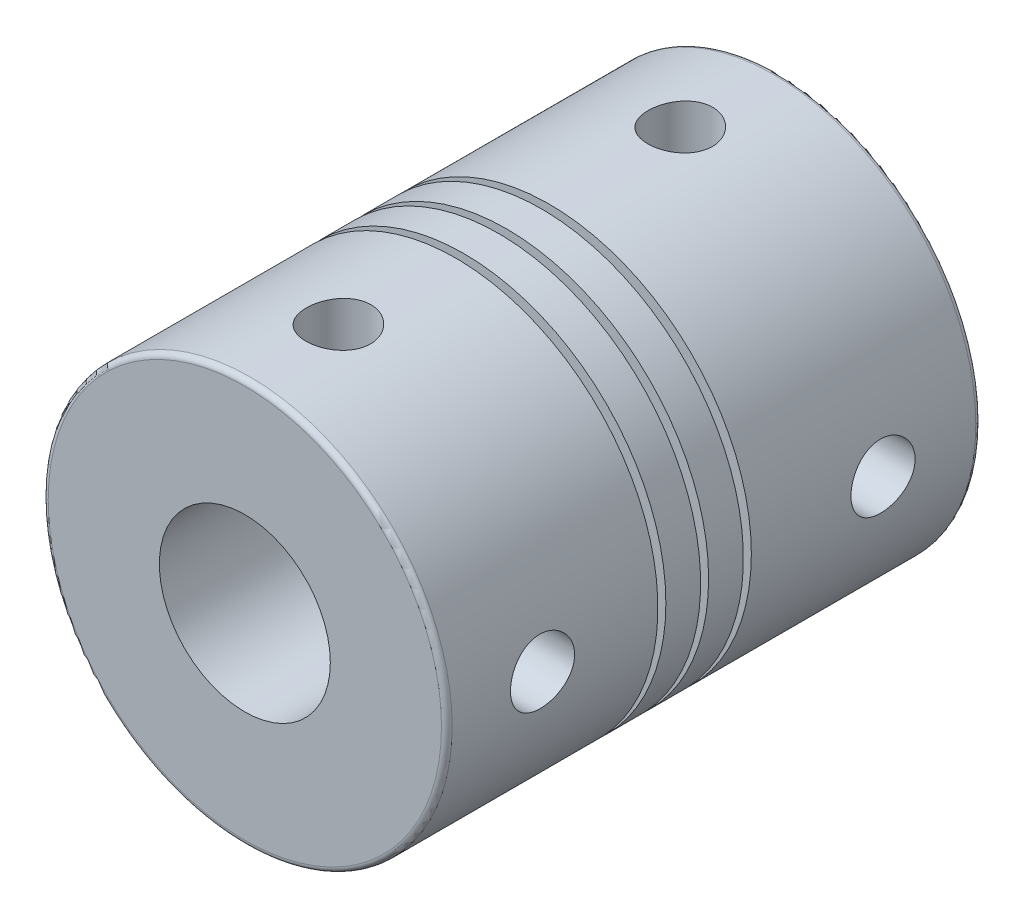
SolidWorks part; units mm, degrees
material "1.4301 (X5CrNi18-10)"
ref_plane "Plan de face" through (0, 0, 0) normal (0, 0, 1) x (1, 0, 0)
ref_plane "Plan de dessus" through (0, 0, 0) normal (0, 1, 0) x (1, 0, 0)
ref_plane "Plan de droite" through (0, 0, 0) normal (1, 0, 0) x (0, 0, -1)
sketch "Esquisse1" plane through (0, 0, 0) normal (0, 0, 1) x (1, 0, 0)
  circle A0 centre (0, 0) radius 9.45
extrude "Boss.-Extru.1" add sketch "Esquisse1" along normal blind 25
fillet "Congé1" radius 0.25 2 edges at (9.45, 0, 0) (9.45, 0, 25)
sketch "Esquisse2" plane through (0, 0, 25) normal (0, 0, 1) x (1, 0, 0)
  circle A0 centre (0, 0) radius 4
extrude "Enlèv. mat.-Extru.1" cut sketch "Esquisse2" against normal blind 17.5
sketch "Esquisse3" plane through (0, 0, 0) normal (0, 0, -1) x (-1, 0, 0)
  circle A0 centre (0, 0) radius 3
extrude "Enlèv. mat.-Extru.2" cut sketch "Esquisse3" against normal blind 17.5
ref_plane "Plan1" through (9.45, 0, 0) normal (1, 0, 0) x (0, 0, -1)
sketch "Esquisse4" plane through (9.45, 0, 0) normal (1, 0, 0) x (0, 0, -1)
  line L0 (-24.75, 0.0829) -> (-0.3596, 0) construction
  line L1 (-24.75, -9.45) -> (-24.75, 9.45) construction
  line L2 (-0.3596, 0) -> (-4.5891, 0.0144) construction
  line L3 (-12.5548, 0.0414) -> (-12.5171, 11.1417) construction
  circle A0 centre (-4.5891, 0.0144) radius 1.5
  circle A1 centre (-20.5204, 0.0685) radius 1.5
extrude "Enlèv. mat.-Extru.3" cut sketch "Esquisse4" against normal blind 10
ref_plane "Plan2" through (0, 9.45, 0) normal (0, 1, 0) x (1, 0, 0)
sketch "Esquisse5" plane through (0, 9.45, 0) normal (0, 1, 0) x (1, 0, 0)
  line L0 (-0.1243, -24.75) -> (-0.1243, -20.4969) construction
  line L1 (9.45, -24.75) -> (-9.45, -24.75) construction
  line L2 (-9.45, -12.5) -> (9.45, -12.5) construction
  line L3 (-9.45, -0.25) -> (-9.45, -24.75) construction
  line L4 (9.45, -10.395) -> (9.45, 10.395) construction
  circle A0 centre (-0.1243, -20.4969) radius 1.5
  circle A1 centre (-0.1243, -4.5031) radius 1.5
extrude "Enlèv. mat.-Extru.4" cut sketch "Esquisse5" against normal blind 10
sketch "Esquisse7" plane through (0, 0, 0) normal (1, 0, 0) x (0, 0, -1)
  line L0 (-13.1242, 9.8339) -> (-13.1242, 8.4942)
  line L1 (-15.1242, 9.8339) -> (-14.7513, 9.8339)
  line L2 (-15.1242, 9.8339) -> (-15.1242, 8.4942)
  line L3 (-15.1242, 8.4942) -> (-14.7513, 8.4942)
  line L4 (-14.7513, 9.8339) -> (-14.7513, 8.4942)
  line L5 (-13.1242, 9.8339) -> (-12.7513, 9.8339)
  line L6 (-12.7513, 9.8339) -> (-12.7513, 8.4942)
  line L7 (-13.1242, 8.4942) -> (-12.7513, 8.4942)
  line L8 (-11.1242, 9.8339) -> (-11.1242, 8.4942)
  line L9 (-11.1242, 9.8339) -> (-10.7513, 9.8339)
  line L10 (-10.7513, 9.8339) -> (-10.7513, 8.4942)
  line L11 (-11.1242, 8.4942) -> (-10.7513, 8.4942)
  line L12 (-25, 0) -> (5.917, 0) construction
  line L13 (-25, 4) -> (-25, -4) construction
  dimension "D1" = 3
revolve "Enlèvement de matière-Révolution1" cut sketch "Esquisse7" angle 360 about L12
